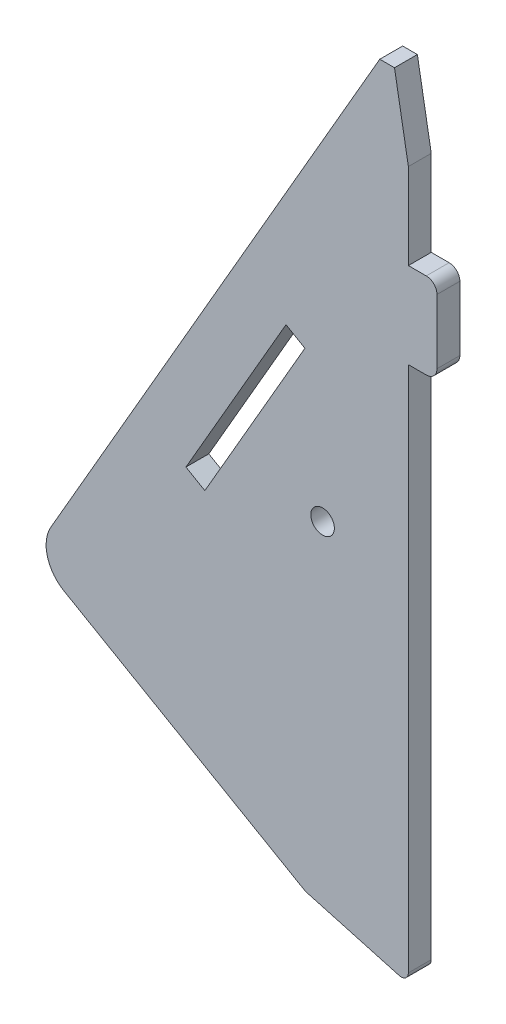
SolidWorks part; units mm, degrees
material "Acrylic (Medium-high impact)"
ref_plane "Front Plane" through (0, 0, 0) normal (0, 0, 1) x (1, 0, 0)
ref_plane "Top Plane" through (0, 0, 0) normal (0, 1, 0) x (1, 0, 0)
ref_plane "Right Plane" through (0, 0, 0) normal (1, 0, 0) x (0, 0, -1)
sketch "Sketch1" plane through (0, 0, 0) normal (0, 0, 1) x (1, 0, 0)
  line L0 (18.8841, -7.966) -> (32.8841, 16.2827)
  line L1404 (1.8301, -31.5045) -> (35.6051, -51.0045)
  line L1432 (18.8841, -7.966) -> (21.5342, -9.496)
  line L1433 (21.5342, -9.496) -> (35.5342, 14.7527)
  line L1434 (35.5342, 14.7527) -> (32.8841, 16.2827)
  line L1462 (46, 55) -> (48.0604, 55)
  line L1463 (50, 44) -> (48.0604, 55)
  line L1484 (35.6051, -51.0045) -> (48.7325, -54.6482)
  line L1485 (50, 44) -> (50, -53.6846)
  line L1486 (0, -24.6743) -> (46, 55)
  circle A0 centre (38, -5) radius 1.65
  arc A1 (0, -24.6743) -> (1.8301, -31.5045) centre (4.3301, -27.1743) ccw
  arc A7 (48.7325, -54.6482) -> (50, -53.6846) centre (49, -53.6846) ccw
  dimension "D1" = 3.3
extrude "Boss-Extrude1" add sketch "Sketch1" along normal blind 3.2
sketch "Sketch2" plane through (0, 0, 3.2) normal (0, 0, 1) x (1, 0, 0)
  line L0 (50, -53.6846) -> (50, 44) construction
  line L1 (50, 32) -> (54, 32)
  line L2 (50, 32) -> (50, 20)
  line L3 (50, 20) -> (54, 20)
  line L4 (54, 32) -> (54, 20)
  dimension "D1" = 4
  dimension "D2" = 12
  dimension "D3" = 12
extrude "Boss-Extrude2" add sketch "Sketch2" against normal up to surface (3.2 mm away) up to face at (39.65, -5, 0)
fillet "Fillet1" radius 1.5 2 edges at (54, 32, 1.6) (54, 20, 1.6)
